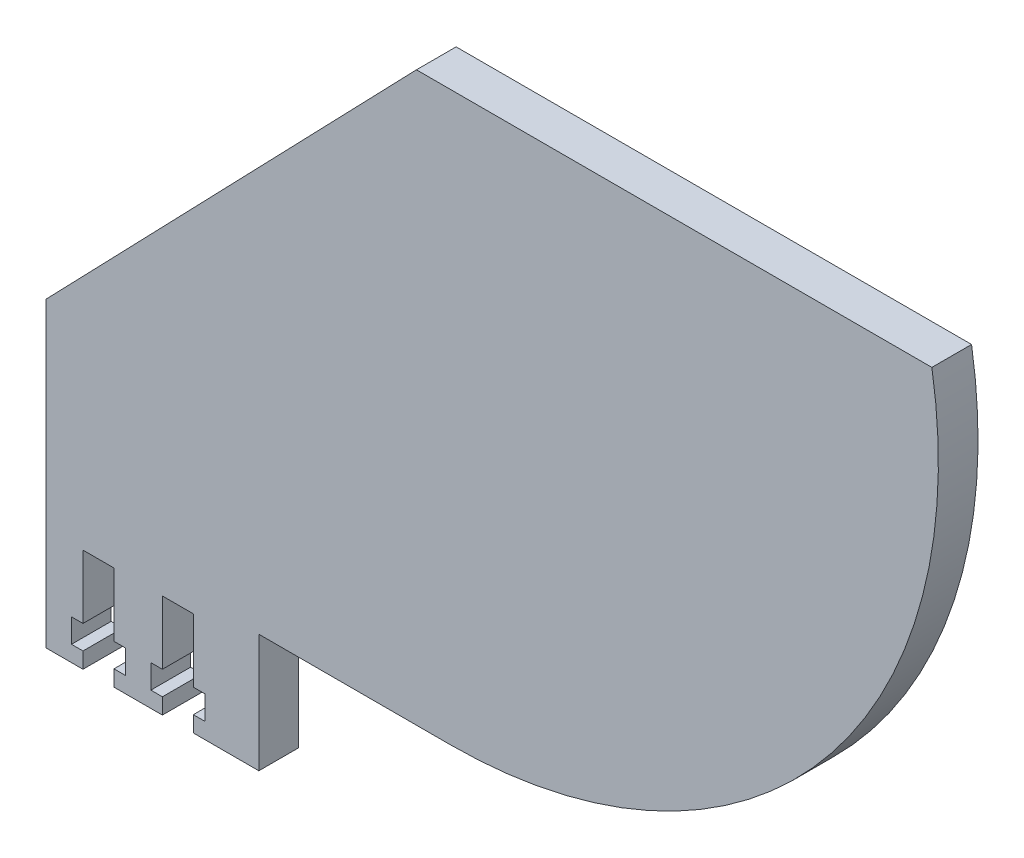
SolidWorks part; units mm, degrees
ref_plane "Front Plane" through (0, 0, 0) normal (0, 0, 1) x (1, 0, 0)
ref_plane "Top Plane" through (0, 0, 0) normal (0, 1, 0) x (1, 0, 0)
ref_plane "Right Plane" through (0, 0, 0) normal (1, 0, 0) x (0, 0, -1)
sketch "Sketch2" plane through (0, 0, 0) normal (0, 0, 1) x (1, 0, 0)
  line L0 (-227.4824, -83.8916) -> (-200.6724, -83.8916)
  line L1 (-200.6724, -83.8916) -> (-200.6724, -68.9916)
  line L2 (-227.4824, -83.8916) -> (-227.4824, -45.8487)
  line L3 (-180.8213, 2.5084) -> (-115.8927, 2.5084)
  line L4 (-200.6724, -68.9916) -> (-176.5743, -68.9916)
  line L5 (-180.8213, 2.5084) -> (-227.4824, -45.8487)
  line L6 (-176.5743, -69.9916) -> (-198.6724, -69.9916) construction
  line L7 (-227.4824, -72.8916) -> (-227.4824, -67.8916) construction
  line L8 (-114.0743, 2.5084) -> (-85.1506, 2.5084) construction
  line L9 (-252.687, -139.258) -> (-67.389, 52.7752) construction
  line L12 (-198.6724, -69.9916) -> (-198.6724, -91.8916) construction
  line L13 (-230.4824, -83.8916) -> (-201.2624, -83.8916) construction
  arc A0 (-176.5743, -68.9916) -> (-115.8927, 2.5084) centre (-176.5743, -7.4916) ccw
  arc A1 (-176.5743, -69.9916) -> (-114.0743, -7.4916) centre (-176.5743, -7.4916) ccw construction
  circle A2 centre (-176.5743, -7.4916) radius 10 construction
  dimension "D1" = 1
  dimension "D2" = 2
extrude "Boss-Extrude1" add sketch "Sketch2" along normal blind 5
sketch "Sketch4" plane through (0, 0, 5) normal (0, 0, 1) x (1, 0, 0)
  line L0 (-212.8224, -83.8916) -> (-208.9224, -83.8916)
  line L1 (-212.8224, -83.8916) -> (-212.8224, -81.8916)
  line L2 (-210.8724, -83.8916) -> (-210.8724, -70.8916) construction
  line L3 (-212.8224, -70.8916) -> (-208.9224, -70.8916)
  line L4 (-212.8224, -78.8916) -> (-214.2724, -78.8916)
  line L5 (-214.2724, -78.8916) -> (-214.2724, -81.8916)
  line L6 (-212.8224, -81.8916) -> (-214.2724, -81.8916)
  line L7 (-212.8224, -78.8916) -> (-212.8224, -70.8916)
  line L8 (-208.9224, -78.8916) -> (-208.9224, -70.8916)
  line L9 (-208.9224, -81.8916) -> (-207.4724, -81.8916)
  line L10 (-207.4724, -78.8916) -> (-207.4724, -81.8916)
  line L11 (-208.9224, -78.8916) -> (-207.4724, -78.8916)
  line L12 (-208.9224, -83.8916) -> (-208.9224, -81.8916)
  line L13 (-222.8224, -83.8916) -> (-218.9224, -83.8916)
  line L14 (-222.8224, -83.8916) -> (-222.8224, -81.8916)
  line L15 (-220.8724, -83.8916) -> (-220.8724, -70.8916) construction
  line L16 (-208.9224, -83.8916) -> (-212.8224, -83.8916) construction
  line L17 (-222.8224, -70.8916) -> (-218.9224, -70.8916)
  line L18 (-222.8224, -78.8916) -> (-224.2724, -78.8916)
  line L19 (-224.2724, -78.8916) -> (-224.2724, -81.8916)
  line L20 (-222.8224, -81.8916) -> (-224.2724, -81.8916)
  line L21 (-222.8224, -78.8916) -> (-222.8224, -70.8916)
  line L22 (-218.9224, -78.8916) -> (-218.9224, -70.8916)
  line L23 (-218.9224, -81.8916) -> (-217.4724, -81.8916)
  line L24 (-217.4724, -78.8916) -> (-217.4724, -81.8916)
  line L25 (-218.9224, -78.8916) -> (-217.4724, -78.8916)
  line L26 (-218.9224, -83.8916) -> (-218.9224, -81.8916)
  line L27 (-218.9224, -83.8916) -> (-222.8224, -83.8916) construction
  line L28 (-200.6724, -83.8916) -> (-200.6724, -68.9916) construction
  dimension "D1" = 3.9
  dimension "D2" = 2
  dimension "D3" = 8
  dimension "D4" = 3
  dimension "D5" = 1.45
  dimension "D6" = 3.9
  dimension "D7" = 2
  dimension "D8" = 8
  dimension "D9" = 3
  dimension "D10" = 1.45
extrude "Cut-Extrude1" cut sketch "Sketch4" against normal blind 5
